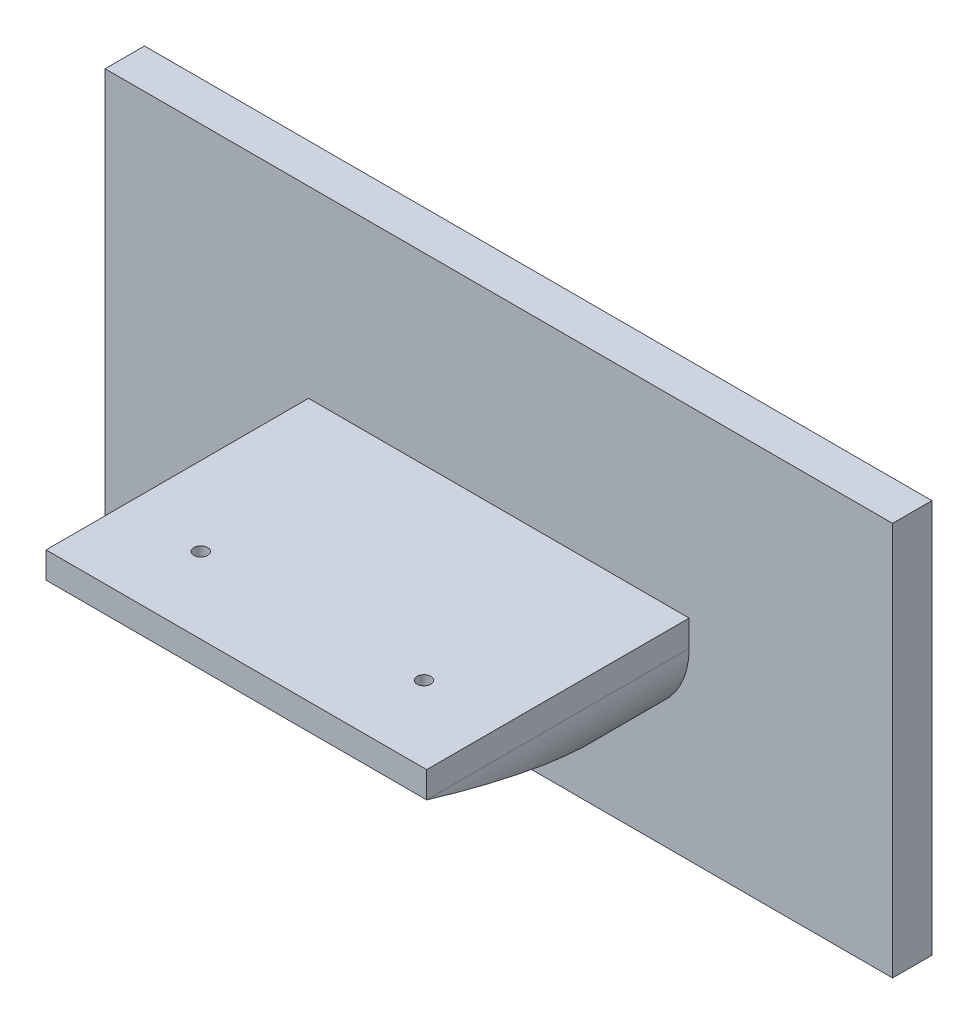
SolidWorks part; units mm, degrees
ref_plane "Front Plane" through (0, 0, 0) normal (0, 0, 1) x (1, 0, 0)
ref_plane "Top Plane" through (0, 0, 0) normal (0, 1, 0) x (1, 0, 0)
ref_plane "Right Plane" through (0, 0, 0) normal (1, 0, 0) x (0, 0, -1)
sketch "Sketch1" plane through (0, 0, 0) normal (0, 0, 1) x (1, 0, 0)
  line L1 (0, 0) -> (300, 0)
  line L2 (0, 0) -> (0, 150)
  line L3 (0, 150) -> (300, 150)
  line L4 (300, 0) -> (300, 150)
  dimension "D1" = 150
  dimension "D2" = 300
extrude "Boss-Extrude1" add sketch "Sketch1" along normal blind 15
sketch "Sketch2" plane through (0, 0, 15) normal (0, 0, 1) x (1, 0, 0)
  line L0 (150, 150) -> (150, 0) construction
  line L1 (77.5, 80) -> (222.5, 80)
  line L2 (77.5, 80) -> (77.5, 70)
  line L3 (107.5, 40) -> (192.5, 40)
  line L4 (222.5, 80) -> (222.5, 70)
  line L5 (300, 150) -> (0, 150) construction
  line L6 (0, 0) -> (300, 0) construction
  arc A0 (222.5, 70) -> (192.5, 40) centre (192.5, 70) cw
  arc A1 (107.5, 40) -> (77.5, 70) centre (107.5, 70) cw
  point P14 (77.5, 40)
  dimension "D4" = 30
  dimension "D1" = 40
  dimension "D2" = 145
  dimension "D3" = 40
extrude "Boss-Extrude2" add sketch "Sketch2" along normal blind 100
sketch "Sketch3" plane through (0, 0, 0) normal (1, 0, 0) x (0, 0, -1)
  line L0 (-115, 70) -> (-15, 40)
  line L1 (-15, 0) -> (-15, 150) construction
  line L2 (-115, 40) -> (-15, 40) construction
  line L3 (-15, 40) -> (-115, 40)
  line L4 (-115, 40) -> (-115, 70)
extrude "Cut-Extrude1" cut sketch "Sketch3" along normal through all
hole_wizard "#5 (0.2055) Diameter Hole1" positions "Sketch4" profile "Sketch6" hole size "#5" standard "ANSI Inch"
sketch "Sketch4" plane through (0, 80, 0) normal (0, 1, 0) x (1, 0, 0)
  line L0 (77.5, -115) -> (77.5, -15) construction
  line L1 (222.5, -115) -> (222.5, -15) construction
  point P0 (107.5, -86.0413)
  point P2 (192.5, -86.0413)
  dimension "D1" = 30
  dimension "D2" = 30
sketch "Sketch6" plane through (107.5, 80, 86.0413) normal (1, 0, 0) x (0, 0, 1)
  line L0 (0, 0) -> (0, 26.5682)
  line L1 (0, 26.5682) -> (2.6098, 25)
  line L2 (2.6098, 25) -> (2.6098, 0)
  line L5 (2.6098, 0) -> (0, 0)
  line L10 (0, 26.5682) -> (-2.6099, 25) construction
  line L11 (0, -6.35) -> (0, 107.95) construction
  dimension "Hole Dia." = 5.2197
  dimension "Hole Depth" = 25
  dimension "Drill Angle" = 118
